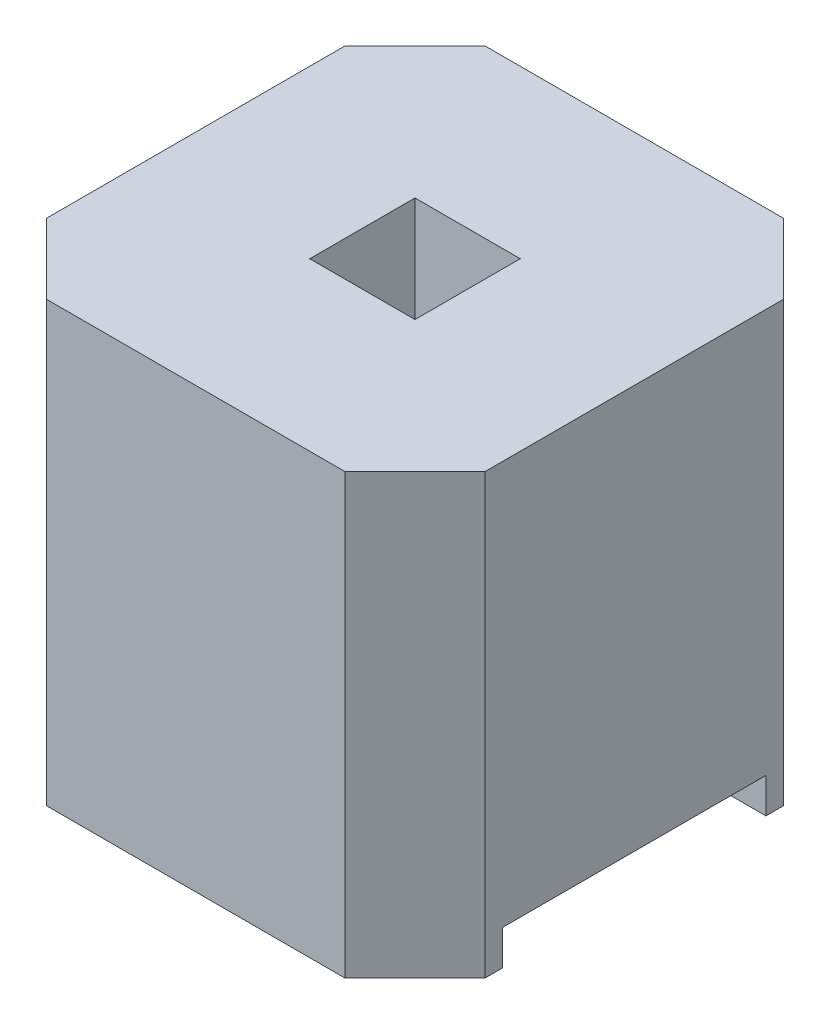
SolidWorks part; units mm, degrees
ref_plane "Plan de face" through (0, 0, 0) normal (0, 0, 1) x (1, 0, 0)
ref_plane "Plan de dessus" through (0, 0, 0) normal (0, 1, 0) x (1, 0, 0)
ref_plane "Plan de droite" through (0, 0, 0) normal (1, 0, 0) x (0, 0, -1)
sketch "Esquisse1" plane through (0, 0, 0) normal (0, 1, 0) x (1, 0, 0)
  line L0 (-1.25, 0.85) -> (-0.85, 1.25)
  line L1 (-0.85, -1.25) -> (0.85, -1.25)
  line L2 (-1.25, -0.85) -> (-1.25, 0.85)
  line L3 (-0.85, 1.25) -> (0.85, 1.25)
  line L4 (1.25, -0.85) -> (1.25, 0.85)
  line L5 (-1.25, -1.25) -> (1.25, 1.25) construction
  line L6 (-1.25, 1.25) -> (1.25, -1.25) construction
  line L7 (0.85, 1.25) -> (1.25, 0.85)
  line L8 (0.85, -1.25) -> (1.25, -0.85)
  line L9 (-1.25, -0.85) -> (-0.85, -1.25)
  line L11 (0.3, 0.3) -> (-0.3, 0.3)
  line L12 (0.3, 0.3) -> (0.3, -0.3)
  line L13 (0.3, -0.3) -> (-0.3, -0.3)
  line L14 (-0.3, 0.3) -> (-0.3, -0.3)
  line L15 (0.3, 0.3) -> (-0.3, -0.3) construction
  line L16 (0.3, -0.3) -> (-0.3, 0.3) construction
  point P0 (0, 0)
  point P14 (0, 0)
  dimension "D1" = 2.5
  dimension "D2" = 2.5
  dimension "D3" = 0.6
extrude "Boss.-Extru.1" add sketch "Esquisse1" along normal blind 2.5
sketch "Esquisse2" plane through (-1.25, 0, 0) normal (-1, 0, 0) x (0, 0, 1)
  line L2 (-0.75, -0.2) -> (0.75, -0.2)
  line L3 (-0.75, -0.2) -> (-0.75, 0.2)
  line L4 (-0.75, 0.2) -> (0.75, 0.2)
  line L5 (0.75, -0.2) -> (0.75, 0.2)
  line L6 (-0.75, -0.2) -> (0.75, 0.2) construction
  line L7 (-0.75, 0.2) -> (0.75, -0.2) construction
  point P0 (0, 0)
  dimension "D1" = 0.2
  dimension "D2" = 1.5
extrude "Enlèv. mat.-Extru.1" cut sketch "Esquisse2" against normal through all
